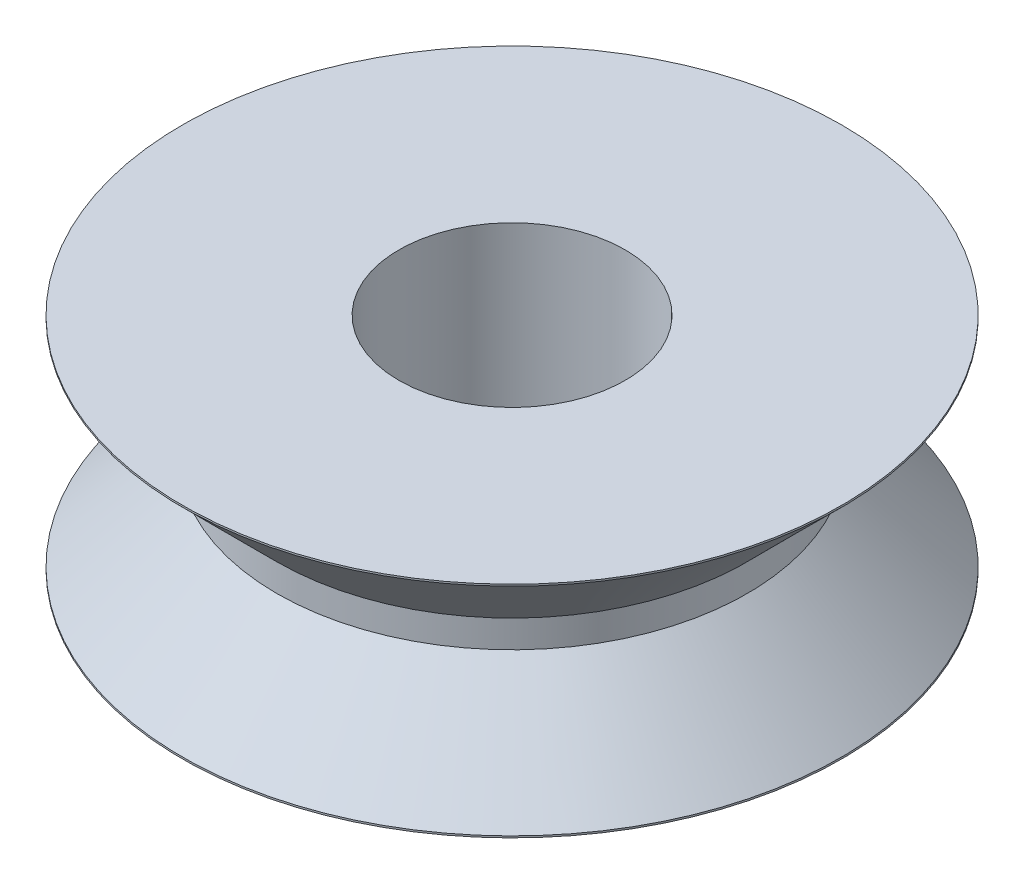
SolidWorks part; units mm, degrees
ref_plane "Front Plane" through (0, 0, 0) normal (0, 0, 1) x (1, 0, 0)
ref_plane "Top Plane" through (0, 0, 0) normal (0, 1, 0) x (1, 0, 0)
ref_plane "Right Plane" through (0, 0, 0) normal (1, 0, 0) x (0, 0, -1)
sketch "Sketch2" plane through (0, 0, 0) normal (0, 0, 1) x (1, 0, 0)
  line L0 (0, 0) -> (19.05, 0)
  line L1 (0, 0) -> (0, 12.7)
  line L2 (0, 12.7) -> (19.05, 12.7)
  line L3 (19.05, 12.7) -> (19.05, 12.6)
  line L4 (19.05, 12.6) -> (13.5937, 7.1437)
  line L5 (13.5937, 7.1437) -> (13.5937, 5.5563)
  line L6 (13.5937, 5.5563) -> (19.05, 0.1)
  line L7 (19.05, 0.1) -> (19.05, 0)
  dimension "D1" = 135
  dimension "D2" = 0.1
  dimension "D3" = 1.5875
  dimension "D4" = 12.7
  dimension "D5" = 19.05
revolve "Revolve1" add sketch "Sketch2" angle 360 about L1
sketch "Sketch7" plane through (0, 12.7, 0) normal (0, 1, 0) x (1, 0, 0)
  circle A0 centre (0, 0) radius 6.5405
  dimension "D1" = 13.081
extrude "Cut-Extrude2" cut sketch "Sketch7" against normal through all
